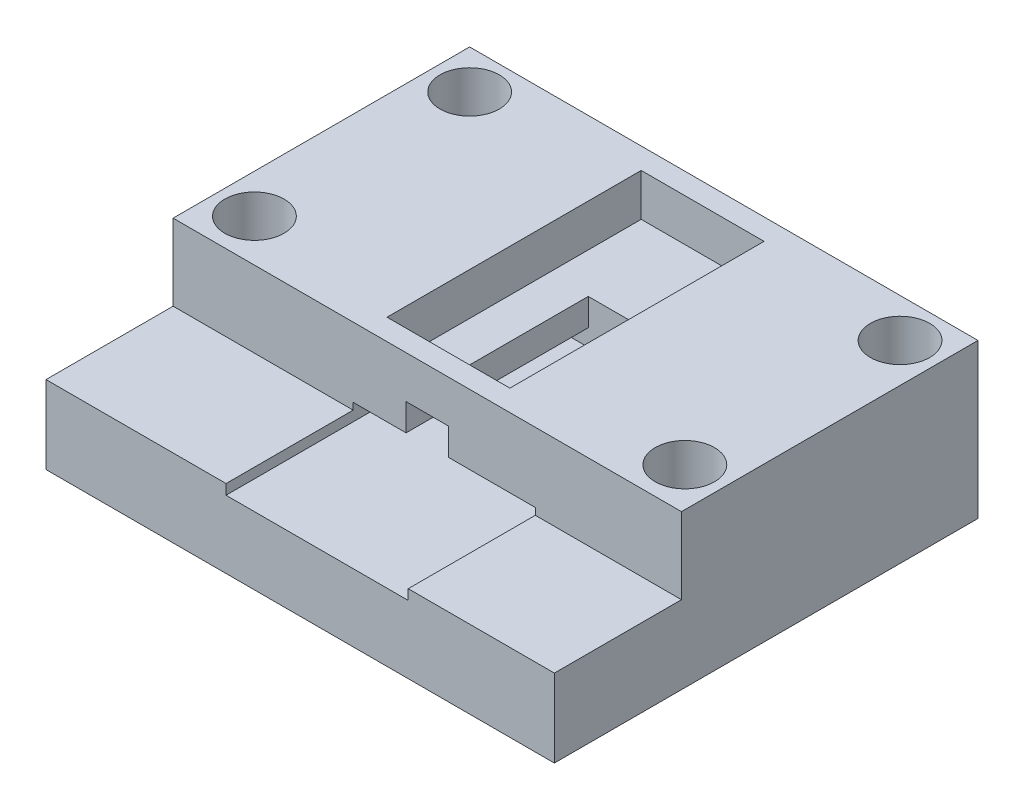
SolidWorks part; units mm, degrees
ref_plane "Front Plane" through (0, 0, 0) normal (0, 0, 1) x (1, 0, 0)
ref_plane "Top Plane" through (0, 0, 0) normal (0, 1, 0) x (1, 0, 0)
ref_plane "Right Plane" through (0, 0, 0) normal (1, 0, 0) x (0, 0, -1)
sketch "Sketch2" plane through (0, 0, 0) normal (0, 1, 0) x (1, 0, 0)
  line L1 (0, 0) -> (60, 0)
  line L2 (0, 0) -> (0, 50)
  line L3 (0, 50) -> (60, 50)
  line L4 (60, 0) -> (60, 50)
  dimension "D1" = 50
  dimension "D2" = 60
extrude "Boss-Extrude1" add sketch "Sketch2" along normal blind 10
sketch "Sketch3" plane through (0, 10, 0) normal (0, 1, 0) x (1, 0, 0)
  line L0 (60, 50) -> (0, 50) construction
  line L1 (21.25, 36.5) -> (42.75, 36.5)
  line L2 (21.25, 36.5) -> (21.25, 0)
  line L3 (21.25, 0) -> (42.75, 0)
  line L4 (42.75, 36.5) -> (42.75, 0)
  line L5 (0, 0) -> (60, 0) construction
  circle A0 centre (30, 32.5) radius 2.25 construction
  point P9 (30, 50)
  dimension "D4" = 4.5
  dimension "D1" = 21.5
  dimension "D3" = 4
  dimension "D5" = 8.75
  dimension "D6" = 17.5
extrude "Cut-Extrude2" cut sketch "Sketch3" against normal blind 2
sketch "Sketch4" plane through (0, 10, 0) normal (0, 1, 0) x (1, 0, 0)
  line L0 (27.5, 50) -> (27.5, 0)
  line L1 (0, 50) -> (60, 50)
  line L2 (0, 50) -> (0, 0)
  line L3 (0, 0) -> (60, 0)
  line L4 (60, 50) -> (60, 0)
  line L5 (32.5, 50) -> (32.5, 0)
  line L6 (27.5, 32.5) -> (32.5, 32.5)
  point P14 (30, 32.5)
  dimension "D1" = 5
extrude "Boss-Extrude2" add sketch "Sketch4" along normal blind 3.2
sketch "Sketch5" plane through (0, 13.2, 0) normal (0, 1, 0) x (1, 0, 0)
  line L1 (0, 50) -> (60, 50)
  line L2 (0, 50) -> (0, 0)
  line L3 (0, 0) -> (60, 0)
  line L4 (60, 50) -> (60, 0)
  line L5 (22.75, 47.5) -> (37.25, 47.5)
  line L6 (22.75, 47.5) -> (22.75, 17.5)
  line L7 (22.75, 17.5) -> (37.25, 17.5)
  line L8 (37.25, 47.5) -> (37.25, 17.5)
  point P4 (30, 47.5)
  point P5 (37.25, 32.5)
  dimension "D1" = 30
  dimension "D2" = 14.5
extrude "Boss-Extrude3" add sketch "Sketch5" along normal blind 5
sketch "Sketch1" plane through (0, 13.2, 0) normal (0, 1, 0) x (1, 0, 0)
  line L5 (4.6, 45.4) -> (55.4, 45.4) construction
  line L6 (4.6, 45.4) -> (4.6, 20) construction
  line L7 (4.6, 20) -> (55.4, 20) construction
  line L8 (55.4, 45.4) -> (55.4, 20) construction
  line L9 (60, 50) -> (0, 50) construction
  line L10 (4.6, 45.4) -> (0, 45.4)
  line L12 (4.6, 45.4) -> (4.6, 50)
  line L13 (0, 50) -> (0, 0) construction
  circle A0 centre (4.6, 20) radius 3.5
  circle A1 centre (4.6, 45.4) radius 3.5
  circle A2 centre (55.4, 45.4) radius 3.5
  circle A3 centre (55.4, 20) radius 3.5
  point P0 (30, 50)
  point P1 (30, 45.4)
  dimension "D3" = 7
  dimension "D1" = 25.4
  dimension "D2" = 50.8
extrude "Cut-Extrude1" cut sketch "Sketch1" against normal through all both and the other way through all contours L12 A1 L10 | L10 A1 L12 | A2 | A0 | A3
sketch "Sketch7" plane through (0, 18.2, 0) normal (0, 1, 0) x (1, 0, 0)
  line L0 (22.75, 17.5) -> (37.25, 17.5) construction
  line L1 (60, 15) -> (0, 15)
  line L2 (60, 15) -> (60, 0)
  line L3 (60, 0) -> (0, 0)
  line L4 (0, 15) -> (0, 0)
  point P4 (0, 0)
  point P6 (0, 0)
  dimension "D1" = 2.5
extrude "Cut-Extrude3" cut sketch "Sketch7" against normal blind 9
